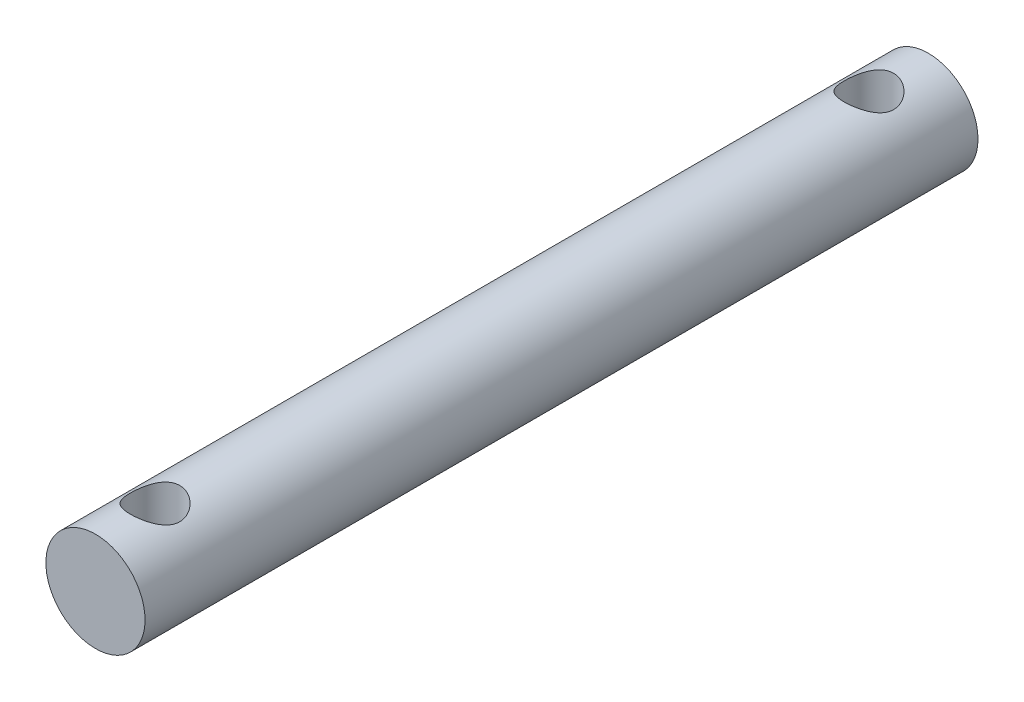
SolidWorks part; units mm, degrees
material "AISI 304"
ref_plane "Front Plane" through (0, 0, 0) normal (0, 0, 1) x (1, 0, 0)
ref_plane "Top Plane" through (0, 0, 0) normal (0, 1, 0) x (1, 0, 0)
ref_plane "Right Plane" through (0, 0, 0) normal (1, 0, 0) x (0, 0, -1)
sketch "Sketch1" plane through (0, 0, 0) normal (0, 0, 1) x (1, 0, 0)
  circle A0 centre (0, 0) radius 2.5
  dimension "D1" = 5
extrude "Boss-Extrude1" add sketch "Sketch1" along normal blind 42
sketch "Sketch2" plane through (0, 0, 0) normal (0, 1, 0) x (1, 0, 0)
  line L0 (2.5, 0) -> (-2.5, 0) construction
  circle A0 centre (0, -3) radius 1.25
  circle A1 centre (0, -39) radius 1.25
  dimension "D1" = 3
  dimension "D2" = 36
extrude "Cut-Extrude1" cut sketch "Sketch2" against normal through all both and the other way through all
